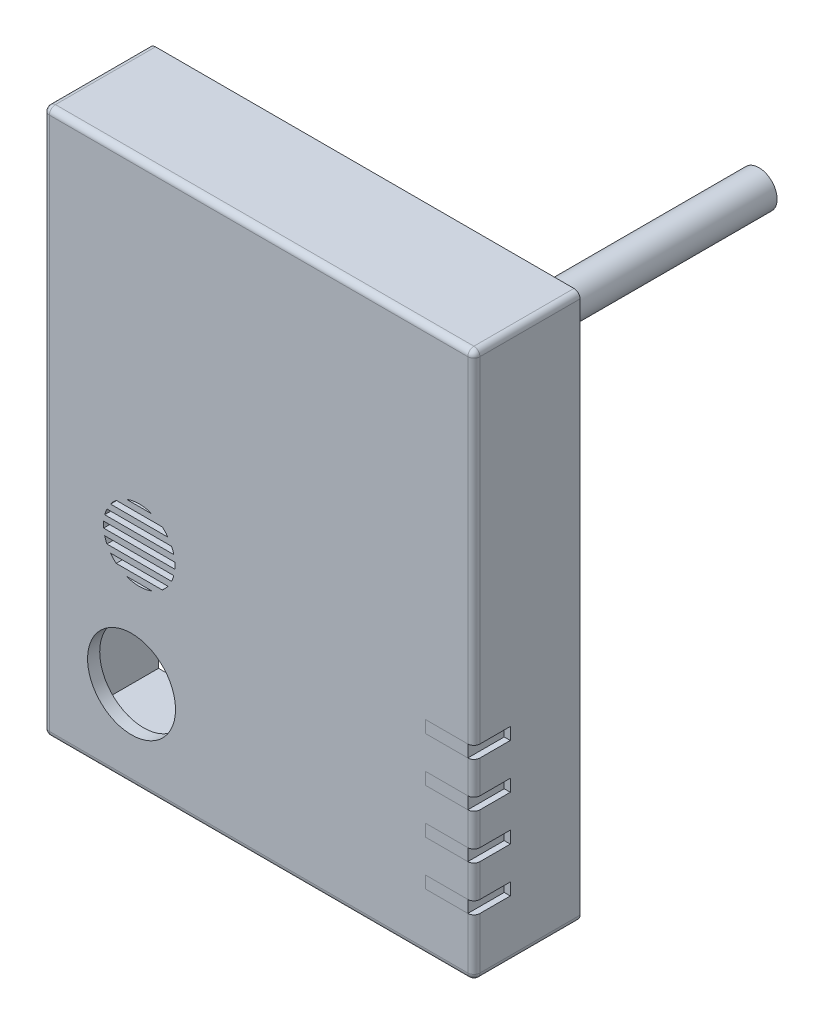
SolidWorks part; units mm, degrees
ref_plane "Front Plane" through (0, 0, 0) normal (0, 0, 1) x (1, 0, 0)
ref_plane "Top Plane" through (0, 0, 0) normal (0, 1, 0) x (1, 0, 0)
ref_plane "Right Plane" through (0, 0, 0) normal (1, 0, 0) x (0, 0, -1)
sketch "Sketch2" plane through (0, 0, 0) normal (0, 0, 1) x (1, 0, 0)
  line L1 (-35.5, 45) -> (35.5, 45)
  line L2 (-35.5, 45) -> (-35.5, -45)
  line L3 (-35.5, -45) -> (35.5, -45)
  line L4 (35.5, 45) -> (35.5, -45)
  line L5 (-35.5, 45) -> (35.5, -45) construction
  line L6 (-35.5, -45) -> (35.5, 45) construction
  point P0 (0, 0)
  dimension "D1" = 90
  dimension "D2" = 71
extrude "Boss-Extrude1" add sketch "Sketch2" along normal blind 17.5 contours L2 L1 L4 L3
shell "Shell1" thickness 3
sketch "Sketch3" plane through (0, 0, 0) normal (0, 0, -1) x (-1, 0, 0)
  line L1 (-32.5, -42) -> (-34, -42)
  line L2 (32.5, -42) -> (34, -42)
  line L3 (-32.5, -42) -> (32.5, -42)
  line L8 (34, -43.5) -> (34, 43.5)
  line L9 (34, 43.5) -> (-34, 43.5)
  line L10 (-34, 43.5) -> (-34, -43.5)
  line L11 (-34, -43.5) -> (34, -43.5)
  line L12 (34, -42) -> (34, 43.5)
  line L13 (34, 43.5) -> (-34, 43.5)
  line L14 (-34, 43.5) -> (-34, -42)
  dimension "D1" = 1.5
sketch "Sketch4" plane through (0, -45, 0) normal (0, -1, 0) x (1, 0, 0)
  line L0 (-35.5, 0) -> (35.5, 0) construction
  line L1 (0, 5.5) -> (7.2, 5.5)
  line L2 (0, 5.5) -> (0, 7.7)
  line L3 (0, 7.7) -> (7.2, 7.7)
  line L4 (7.2, 5.5) -> (7.2, 7.7)
  line L5 (-35.5, 17.5) -> (-35.5, 0) construction
  dimension "D1" = 7.2
  dimension "D2" = 2.2
  dimension "D3" = 5.5
  dimension "D4" = 35.5
extrude "Cut-Extrude10" cut sketch "Sketch3" against normal blind 1.5 contours L14 L1 L3 L2 L12 L13
extrude "Cut-Extrude2" cut sketch "Sketch4" against normal blind 2
sketch "Sketch5" plane through (0, 0, 17.5) normal (0, 0, 1) x (1, 0, 0)
  line L0 (35.5, 45) -> (35.5, -45) construction
  line L1 (35.5, -35.5) -> (27.5, -35.5)
  line L2 (35.5, -35.5) -> (35.5, -33.5)
  line L3 (35.5, -33.5) -> (27.5, -33.5)
  line L4 (27.5, -35.5) -> (27.5, -33.5)
  line L5 (-35.5, -45) -> (35.5, -45) construction
  dimension "D1" = 2
  dimension "D2" = 8
  dimension "D3" = 9.5
sketch "Sketch6" plane through (35.5, 0, 0) normal (1, 0, 0) x (0, 0, -1)
  line L0 (-17.5, -35.5) -> (-17.5, -33.5) construction
  line L1 (-17.5, -35.5) -> (-11.5, -35.5)
  line L2 (-17.5, -35.5) -> (-17.5, -33.5)
  line L3 (-17.5, -33.5) -> (-11.5, -33.5)
  line L4 (-11.5, -35.5) -> (-11.5, -33.5)
  line L5 (-17.5, 45) -> (-17.5, -45) construction
  dimension "D1" = 6
  dimension "D2" = 9.5
extrude "Cut-Extrude3" cut sketch "Sketch5" against normal blind 2
extrude "Cut-Extrude4" cut sketch "Sketch6" against normal up to surface (3 mm away) up to face at (32.5, -11.5, 10.8333)
pattern_linear "LPattern1" count 4 spacing 7.4 along (0, 1, 0) of "Cut-Extrude4", "Cut-Extrude3"
sketch "Sketch7" plane through (0, 0, 17.5) normal (0, 0, 1) x (1, 0, 0)
  line L0 (-35.5, 45) -> (-35.5, -45) construction
  line L1 (-35.5, -45) -> (35.5, -45) construction
  circle A0 centre (-20.95, -30.48) radius 7.25
  dimension "D3" = 14.5
  dimension "D1" = 14.55
  dimension "D2" = 14.52
extrude "Cut-Extrude5" cut sketch "Sketch7" against normal up to surface (2 mm away) up to face at (24, -18.72, 15.5)
sketch "Sketch8" plane through (0, 0, 17.5) normal (0, 0, 1) x (1, 0, 0)
  line L0 (-35.5, 45) -> (-35.5, -45) construction
  line L1 (-35.5, -45) -> (35.5, -45) construction
  line L2 (-13.79, -10) -> (-25.57, -10) construction
  line L3 (-25.5487, -9.5) -> (-13.8113, -9.5)
  line L4 (-25.3758, -8.5) -> (-13.9842, -8.5)
  line L5 (-25.0131, -7.5) -> (-14.3469, -7.5)
  line L6 (-24.4173, -6.5) -> (-14.9427, -6.5)
  line L7 (-23.4803, -5.5) -> (-15.8797, -5.5)
  line L8 (-21.7876, -4.5) -> (-17.5724, -4.5)
  line L9 (-21.7876, -15.5) -> (-17.5724, -15.5)
  line L10 (-23.4803, -14.5) -> (-15.8797, -14.5)
  line L11 (-24.4173, -13.5) -> (-14.9427, -13.5)
  line L12 (-25.0131, -12.5) -> (-14.3469, -12.5)
  line L13 (-25.3758, -11.5) -> (-13.9842, -11.5)
  line L14 (-25.5487, -10.5) -> (-13.8113, -10.5)
  circle A0 centre (-19.68, -10) radius 5.89
  dimension "D3" = 11.78
  dimension "D1" = 15.82
  dimension "D2" = 35
  dimension "D4" = 0.5
  dimension "D5" = 1
  dimension "D6" = 1
  dimension "D7" = 1
  dimension "D8" = 1
  dimension "D9" = 1
extrude "Cut-Extrude7" cut sketch "Sketch8" against normal up to surface (2 mm away) contours L2 A0 L3 | A0 L2 L14 | L4 A0 L5 | L13 A0 L12 | L11 A0 L10 | L6 A0 L7 | L8 A0 | L9 A0 up to face at (-28.2, -30.48, 15.5)
fillet "Fillet1" radius 1 18 edges at (32.5, -38.75, 15.5) (32.5, -30.8, 15.5) (32.5, -23.4, 15.5) (32.5, -16, 15.5) (0, 42, 15.5) (32.5, 15.35, 15.5) (35.5, -45, 8.75) (35.5, 45, 8.75) (-35.5, 45, 8.75) (-35.5, -45, 8.75) (35.5, -40.25, 17.5) (35.5, -30.8, 17.5) (35.5, -23.4, 17.5) (35.5, -16, 17.5) (35.5, 16.85, 17.5) (0, 45, 17.5) (-35.5, 0, 17.5) (0, -45, 17.5)
fillet "Fillet2" radius 1 6 edges at (-0.5, -42, 15.5) (-32.5, -0.5, 15.5) (32.5, -42, 8) (32.2071, -42, 15.2071) (-32.5, 42, 8) (-32.5, 41.7071, 15.2071)
sketch "Sketch9" plane through (0, 0, 17.5) normal (0, 0, 1) x (1, 0, 0)
  line L0 (35.5, 44) -> (35.5, -11.3) construction
  line L1 (-34.5, 45) -> (34.5, 45) construction
  circle A0 centre (20.5, 30) radius 3
  dimension "D1" = 6
  dimension "D2" = 15
  dimension "D3" = 15
extrude "Boss-Extrude2" add sketch "Sketch9" against normal blind 62
sketch "Sketch12" plane through (0, 0, 17.5) normal (0, 0, 1) x (1, 0, 0)
  line L0 (35.5, 44) -> (35.5, -11.3) construction
  line L1 (-34.5, 45) -> (34.5, 45) construction
  circle A0 centre (20.5, 30) radius 3.6 construction
  dimension "D1" = 7.2
  dimension "D2" = 15
  dimension "D3" = 15
sketch "Sketch20" plane through (0, 0, -44.5) normal (0, 0, -1) x (-1, 0, 0)
  circle A0 centre (-20.5, 30) radius 1.2 construction
hole_wizard "Ø3.0 (3) Diameter Hole1" positions "3DSketch4" profile "Sketch21" hole size "Ø3.0" standard "JIS"
sketch3d "3DSketch4"
  point P0 (20.5, 30, -44.5)
sketch "Sketch21" plane through (20.5, 30, -44.5) normal (1, 0, 0) x (0, 1, 0)
  line L0 (0, 0) -> (0, 6.9013)
  line L1 (0, 6.9013) -> (1.5, 6)
  line L2 (1.5, 6) -> (1.5, 0)
  line L5 (1.5, 0) -> (0, 0)
  line L10 (0, 6.9013) -> (-1.5, 6) construction
  line L11 (0, -6.35) -> (0, 107.95) construction
  dimension "Hole Dia." = 3
  dimension "Hole Depth" = 6
  dimension "Drill Angle" = 118
sketch "Sketch33" plane through (0, 0, 0) normal (0, 0, -1) x (-1, 0, 0)
  line L0 (-34, -42) -> (-35.5, -42) construction
  line L1 (-35.5, 44) -> (-35.5, -44) construction
sketch "Sketch34" plane through (35.5, 0, 0) normal (1, 0, 0) x (0, 0, -1)
  line L0 (0, -42) -> (-4.3816, -42) construction
  line L1 (0, -42) -> (-1.5, -42)
  line L2 (-1.5, -42) -> (-1.5, -44)
  line L3 (-1.5, -44) -> (0, -43.5)
  line L4 (0, 44) -> (0, -44) construction
  line L5 (0, -43.5) -> (0, -42)
  dimension "D1" = 1.5
  dimension "D2" = 2
  dimension "D3" = 1.5
extrude "Cut-Extrude13" cut sketch "Sketch34" against normal up to surface (68 mm away) from surface at -1.5 up to face at (-34, 0.75, 0.75) starting at face at (34, 0.75, 0.75)
sketch "Sketch35" plane through (0, 0, 17.5) normal (0, 0, 1) x (1, 0, 0)
  line L0 (27.5, -35.5) -> (27.5, -33.5)
  line L1 (27.5, -33.5) -> (34.5, -33.5)
  line L2 (34.5, -33.5) -> (34.5, -35.5)
  line L3 (34.5, -35.5) -> (27.5, -35.5)
extrude "Boss-Extrude3" add sketch "Sketch35" against normal up to vertex (6 mm away) separate body
pattern_linear "LPattern2" count 4 spacing 7.4 along (0, 1, 0) of "Boss-Extrude3"
